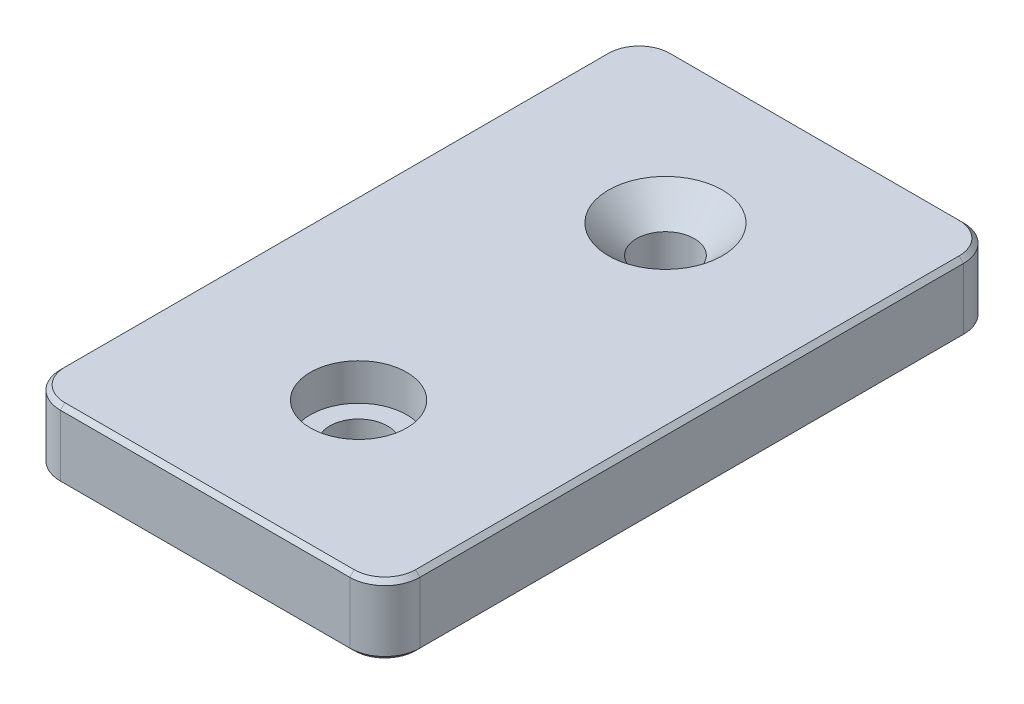
SolidWorks part; units mm, degrees
ref_plane "Front Plane" through (0, 0, 0) normal (0, 0, 1) x (1, 0, 0)
ref_plane "Top Plane" through (0, 0, 0) normal (0, 1, 0) x (1, 0, 0)
ref_plane "Right Plane" through (0, 0, 0) normal (1, 0, 0) x (0, 0, -1)
sketch "Sketch1" plane through (0, 0, 0) normal (0, 1, 0) x (1, 0, 0)
  line L1 (-20.5, -35) -> (20.5, -35)
  line L2 (-20.5, -35) -> (-20.5, 35)
  line L3 (-20.5, 35) -> (20.5, 35)
  line L4 (20.5, -35) -> (20.5, 35)
  line L5 (-20.5, -35) -> (20.5, 35) construction
  line L6 (-20.5, 35) -> (20.5, -35) construction
  circle A0 centre (0, 17.5) radius 3.3
  circle A1 centre (0, -17.5) radius 3.3
  point P0 (0, 0)
  dimension "D3" = 6.6
  dimension "D4" = 6.6
  dimension "D1" = 41
  dimension "D2" = 70
  dimension "D5" = 17.5
  dimension "D6" = 17.5
extrude "Boss-Extrude1" add sketch "Sketch1" along normal blind 8
sketch "Sketch2" plane through (0, 8, 0) normal (0, 1, 0) x (1, 0, 0)
  circle A0 centre (0, -17.5) radius 5.5
extrude "Cut-Extrude1" cut sketch "Sketch2" against normal blind 4.2
chamfer "Chamfer2" distance 3.2 angle 45 1 edges at (0, 8, -14.2)
fillet "Fillet1" radius 4 4 edges at (-20.5, 4, 35) (20.5, 4, 35) (20.5, 4, -35) (-20.5, 4, -35)
chamfer "Chamfer4" distance 0.5 angle 45 16 edges at (-20.5, 0, 0) (-19.3284, 0, 33.8284) (0, 0, 35) (19.3284, 0, 33.8284) (20.5, 0, 0) (-19.3284, 0, -33.8284) (19.3284, 0, -33.8284) (0, 0, -35) (-20.5, 8, 0) (-19.3284, 8, 33.8284) (0, 8, 35) (19.3284, 8, 33.8284) (20.5, 8, 0) (19.3284, 8, -33.8284) (0, 8, -35) (-19.3284, 8, -33.8284)
